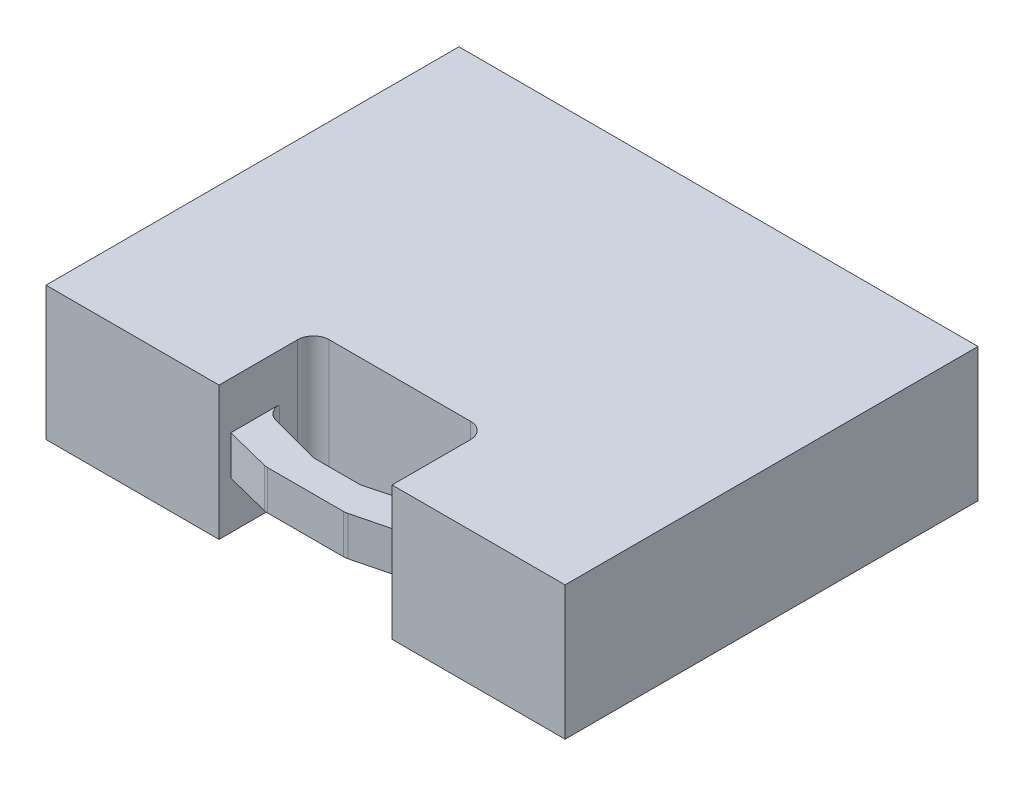
SolidWorks part; units mm, degrees
ref_plane "Front Plane" through (0, 0, 0) normal (0, 0, 1) x (1, 0, 0)
ref_plane "Top Plane" through (0, 0, 0) normal (0, 1, 0) x (1, 0, 0)
ref_plane "Right Plane" through (0, 0, 0) normal (1, 0, 0) x (0, 0, -1)
sketch "Sketch1" plane through (0, 0, 0) normal (0, 1, 0) x (1, 0, 0)
  line L1 (-209.55, -166.6875) -> (209.55, -166.6875)
  line L2 (-209.55, -166.6875) -> (-209.55, 166.6875)
  line L3 (-209.55, 166.6875) -> (209.55, 166.6875)
  line L4 (209.55, -166.6875) -> (209.55, 166.6875)
  line L5 (-209.55, -166.6875) -> (209.55, 166.6875) construction
  line L6 (-209.55, 166.6875) -> (209.55, -166.6875) construction
  point P0 (0, 0)
  dimension "D1" = 333.375
  dimension "D2" = 419.1
extrude "Boss-Extrude1" add sketch "Sketch1" along normal blind 107.95
sketch "Sketch2" plane through (0, 107.95, 0) normal (0, 1, 0) x (1, 0, 0)
  line L0 (0, 0) -> (0, -115.8875) construction
  line L1 (-69.85, -141.2875) -> (69.85, -141.2875)
  line L2 (-69.85, -141.2875) -> (-69.85, -90.4875)
  line L3 (-69.85, -90.4875) -> (69.85, -90.4875)
  line L4 (69.85, -141.2875) -> (69.85, -90.4875)
  line L5 (-69.85, -141.2875) -> (69.85, -90.4875) construction
  line L6 (-69.85, -90.4875) -> (69.85, -141.2875) construction
  line L7 (-209.55, -166.6875) -> (209.55, -166.6875) construction
  line L8 (-69.85, -166.6875) -> (-69.85, -157.1625)
  line L9 (-69.85, -157.1625) -> (-32.169, -166.6875)
  line L10 (-32.169, -166.6875) -> (-69.85, -166.6875)
  line L11 (-69.85, -157.1625) -> (-69.85, -141.2875) construction
  line L12 (0, -166.6875) -> (0, -141.2875) construction
  line L13 (69.85, -157.1625) -> (69.85, -141.2875) construction
  line L14 (32.169, -166.6875) -> (69.85, -166.6875)
  line L15 (69.85, -157.1625) -> (32.169, -166.6875)
  line L16 (69.85, -166.6875) -> (69.85, -157.1625)
  point P0 (0, -115.8875)
  dimension "D1" = 139.7
  dimension "D2" = 50.8
  dimension "D3" = 50.8
  dimension "D4" = 9.525
extrude "Cut-Extrude1" cut sketch "Sketch2" against normal through all
chamfer "Chamfer1" distance 50.8 angle 15 2 edges at (69.85, 53.975, 141.2875) (-69.85, 53.975, 141.2875)
fillet "Fillet1" radius 12.7 8 edges at (32.169, 53.975, 166.6875) (-32.169, 53.975, 166.6875) (69.85, 53.975, 127.6757) (19.05, 53.975, 141.2875) (-19.05, 53.975, 141.2875) (-69.85, 53.975, 127.6757) (69.85, 53.975, 90.4875) (-69.85, 53.975, 90.4875)
sketch "Sketch3" plane through (0, 107.95, 0) normal (0, 1, 0) x (1, 0, 0)
  line L1 (-69.85, -166.6875) -> (69.85, -166.6875)
  line L2 (-69.85, -166.6875) -> (-69.85, -110.2845)
  line L3 (-69.85, -110.2845) -> (69.85, -110.2845)
  line L4 (69.85, -166.6875) -> (69.85, -110.2845)
extrude "Cut-Extrude2" cut sketch "Sketch3" against normal blind 38.1
sketch "Sketch4" plane through (0, 0, 0) normal (0, -1, 0) x (1, 0, 0)
  line L0 (69.85, 117.9306) -> (69.85, 103.1875) construction
  line L1 (-69.85, 166.6875) -> (69.85, 166.6875)
  line L2 (-69.85, 166.6875) -> (-69.85, 110.5591)
  line L3 (-69.85, 110.5591) -> (69.85, 110.5591)
  line L4 (69.85, 166.6875) -> (69.85, 110.5591)
extrude "Cut-Extrude3" cut sketch "Sketch4" against normal blind 38.1
